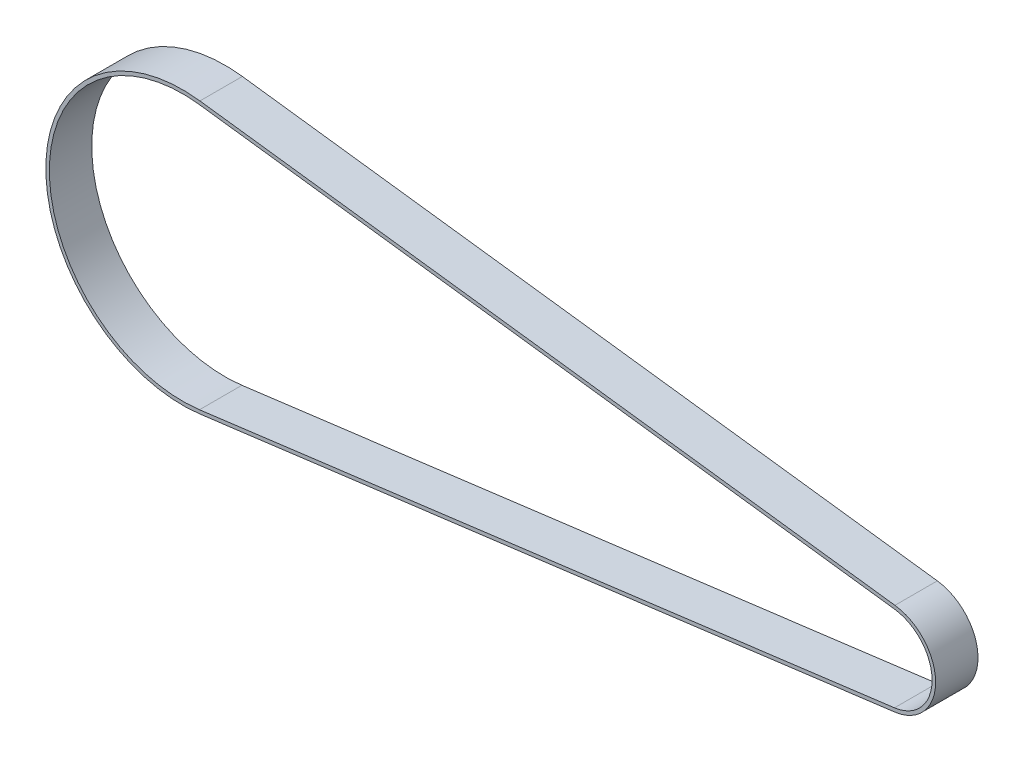
SolidWorks part; units mm, degrees
material "Caucho"
ref_plane "Alzado" through (0, 0, 0) normal (0, 0, 1) x (1, 0, 0)
ref_plane "Planta" through (0, 0, 0) normal (0, 1, 0) x (1, 0, 0)
ref_plane "Vista lateral" through (0, 0, 0) normal (1, 0, 0) x (0, 0, -1)
sketch "Croquis1" plane through (0, 0, 0) normal (0, 0, 1) x (1, 0, 0)
  line L0 (2.4034, 18.6962) -> (100.7777, 6.0502)
  line L1 (0, 0) -> (79.1587, 0) construction
  line L2 (100.7777, -6.0502) -> (2.4034, -18.6962)
  line L3 (100.8415, -6.5461) -> (2.4671, -19.1921)
  line L4 (2.4671, 19.1921) -> (100.8415, 6.5461)
  arc A0 (2.4034, 18.6962) -> (2.4034, -18.6962) centre (0, 0) ccw
  arc A1 (100.7777, -6.0502) -> (100.7777, 6.0502) centre (100, 0) ccw
  arc A2 (2.4671, 19.1921) -> (2.4671, -19.1921) centre (0, 0) ccw
  arc A3 (100.8415, -6.5461) -> (100.8415, 6.5461) centre (100, 0) ccw
  dimension "D1" = 12.2
  dimension "D2" = 37.7
  dimension "D3" = 100
  dimension "D4" = 0.5
extrude "Saliente-Extruir1" add sketch "Croquis1" along normal blind 6
